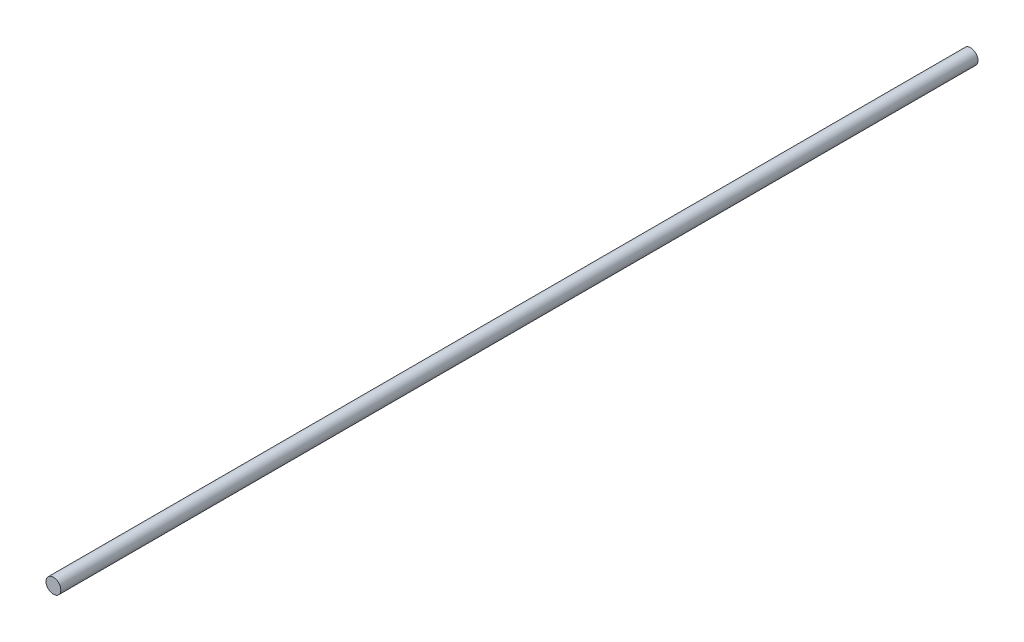
SolidWorks part; units mm, degrees
material "Cast Carbon Steel"
ref_plane "Front Plane" through (0, 0, 0) normal (0, 0, 1) x (1, 0, 0)
ref_plane "Top Plane" through (0, 0, 0) normal (0, 1, 0) x (1, 0, 0)
ref_plane "Right Plane" through (0, 0, 0) normal (1, 0, 0) x (0, 0, -1)
sketch "Sketch1" plane through (0, 0, 0) normal (0, 0, 1) x (1, 0, 0)
  circle A0 centre (0, 0) radius 2.5
  dimension "D1" = 5
extrude "Boss-Extrude1" add sketch "Sketch1" along normal blind 310
cosmetic thread "Cosmetic Thread1" parameters "D2"=4.11
